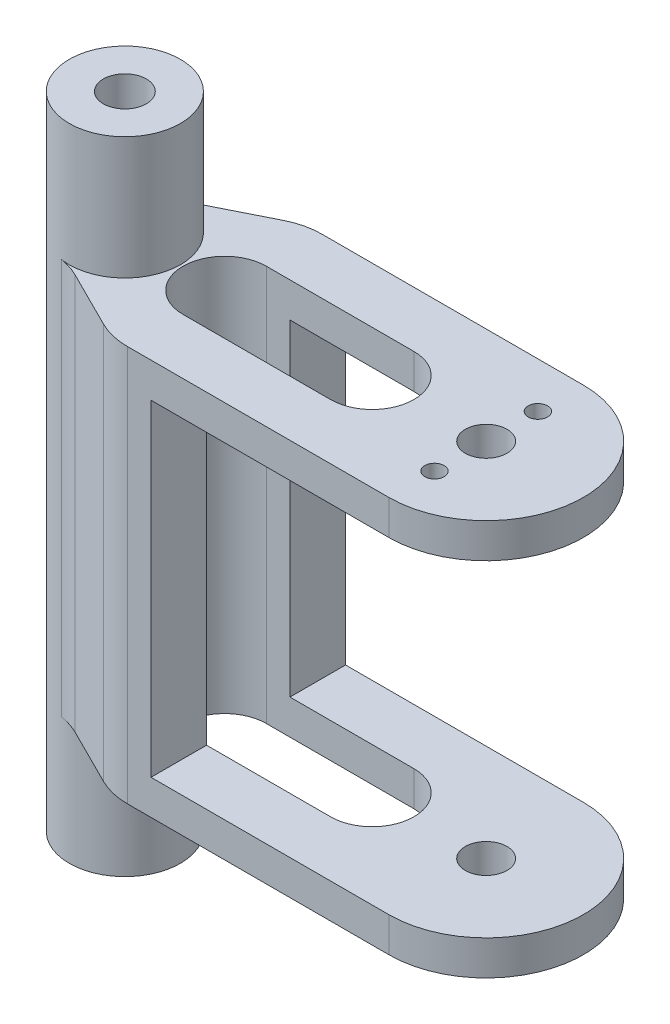
SolidWorks part; units mm, degrees
ref_plane "Front Plane" through (0, 0, 0) normal (0, 0, 1) x (1, 0, 0)
ref_plane "Top Plane" through (0, 0, 0) normal (0, 1, 0) x (1, 0, 0)
ref_plane "Right Plane" through (0, 0, 0) normal (1, 0, 0) x (0, 0, -1)
sketch "Sketch1" plane through (0, 0, 0) normal (0, 1, 0) x (1, 0, 0)
  line L0 (-22.942, 14) -> (-62.942, 14)
  line L1 (-62.942, 14) -> (-62.942, -14)
  line L2 (-62.942, -14) -> (-22.942, -14)
  circle A0 centre (-22.942, 0) radius 3
  circle A1 centre (-22.942, 0) radius 14
extrude "Boss-Extrude4" add sketch "Sketch1" along normal blind 5 contours A1 L0 L1 L2 | A1 A0
sketch "Sketch4" plane through (0, 5, 0) normal (0, 1, 0) x (1, 0, 0)
  line L0 (-22.942, 14) -> (-62.942, 14) construction
  line L1 (-62.942, -14) -> (-57.1806, -14)
  line L2 (-62.942, -14) -> (-62.942, 14)
  line L3 (-62.942, 14) -> (-57.1806, 14)
  line L4 (-57.1806, -14) -> (-57.1806, 14)
extrude "Boss-Extrude5" add sketch "Sketch4" along normal blind 47
sketch "Sketch6" plane through (0, 52, 0) normal (0, 1, 0) x (1, 0, 0)
  line L0 (-22.942, 14) -> (-62.942, 14)
  line L1 (-62.942, 14) -> (-62.942, -14)
  line L2 (-62.942, -14) -> (-22.942, -14)
  circle A0 centre (-22.942, 0) radius 3
  circle A1 centre (-22.942, 0) radius 14
  point P7 (-62.942, 14)
  point P9 (-62.942, -14)
  line M4 (-62.942, 14) -> (-62.942, -14)
  line M5 (-62.942, -14) -> (-57.1806, -14)
  line M6 (-57.1806, -14) -> (-57.1806, 14)
  line M7 (-57.1806, 14) -> (-62.942, 14)
extrude "Boss-Extrude6" add sketch "Sketch6" along normal blind 5 contours A1 L0 L2 M6 | M7 M4 M5 M6 | A1 A0
sketch "Sketch8" plane through (0, 57, 0) normal (0, 1, 0) x (1, 0, 0)
  line L0 (-22.942, 0) -> (-74.942, 0)
  circle A0 centre (-74.942, 0) radius 3.1
  circle A1 centre (-74.942, 0) radius 8
extrude "Boss-Extrude7" add sketch "Sketch8" along normal blind 17.61 and the other way blind 74.61 separate body
sketch "Sketch11" plane through (0, 0, 0) normal (0, -1, 0) x (1, 0, 0)
  line L0 (-74.942, 8) -> (-62.942, 14)
  line L1 (-74.942, -8) -> (-62.942, -14)
  line L2 (-62.942, -14) -> (-62.942, 14)
  circle A0 centre (-74.942, 0) radius 8 construction
  arc A1 (-74.942, 8) -> (-74.942, -8) centre (-74.942, 0) cw
  circle A2 centre (-74.942, 0) radius 8
  arc A3 (-74.942, 8) -> (-74.942, -8) centre (-74.942, 0) ccw
  line M2 (-62.942, 14) -> (-62.942, -14)
  dimension "D1" = 0
extrude "Boss-Extrude8" add sketch "Sketch11" against normal blind 57 contours L0 A1 L1 M2
fillet "Fillet1" radius 10 2 edges at (-62.942, 28.5, -14) (-62.942, 28.5, 14)
fillet "Fillet2" radius 10 2 edges at (-74.942, 28.5, 8) (-74.942, 28.5, -8)
sketch "Sketch13" plane through (0, 0, 0) normal (0, -1, 0) x (1, 0, 0)
  line L0 (-60.5814, -14) -> (-60.5814, 14)
  line L1 (-22.942, 0) -> (-60.5814, 0) construction
  line L2 (-22.942, -6) -> (-60.5814, -6)
  line L3 (-22.942, 6) -> (-60.5814, 6)
  line L4 (-60.5814, 0) -> (-39.3384, 0) construction
  line L5 (-60.5814, 6) -> (-39.3384, 6)
  line L6 (-60.5814, -6) -> (-39.3384, -6)
  arc A0 (-22.942, -6) -> (-22.942, 6) centre (-22.942, 0) ccw
  arc A1 (-60.5814, 6) -> (-60.5814, -6) centre (-60.5814, 0) ccw
  arc A2 (-60.5814, 6) -> (-60.5814, -6) centre (-60.5814, 0) ccw
  arc A3 (-39.3384, -6) -> (-39.3384, 6) centre (-39.3384, 0) ccw
  point P7 (-41.7617, 0)
  point P14 (-49.9599, 0)
extrude "Cut-Extrude1" cut sketch "Sketch13" against normal blind 57 contours A3 L5 A2 L6
sketch "Sketch14" plane through (0, 57, 0) normal (0, 1, 0) x (1, 0, 0)
  line L0 (-22.942, 0) -> (-22.942, -7.4422)
  line L1 (-22.942, 0) -> (-22.942, 7.4422)
  circle A0 centre (-22.942, 7.4422) radius 1.395
  circle A1 centre (-22.942, -7.4422) radius 1.395
extrude "Cut-Extrude2" cut sketch "Sketch14" against normal blind 3 contours A1 | A0
